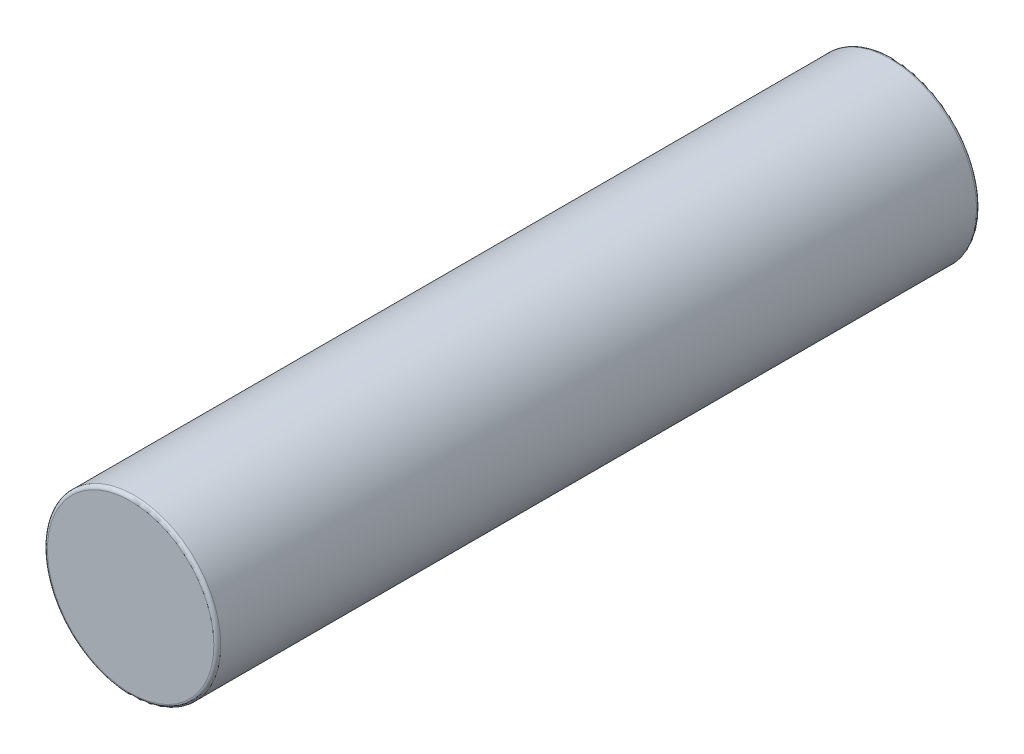
SolidWorks part; units mm, degrees
ref_plane "Front" through (0, 0, 0) normal (0, 0, 1) x (1, 0, 0)
ref_plane "Top" through (0, 0, 0) normal (0, 1, 0) x (1, 0, 0)
ref_plane "Right" through (0, 0, 0) normal (1, 0, 0) x (0, 0, -1)
sketch "Sketch1" plane through (0, 0, 0) normal (0, 0, 1) x (1, 0, 0)
  circle A0 centre (0, 0) radius 1.25
  dimension "D1" = 2.5
extrude "Boss-Extrude1" add sketch "Sketch1" along normal blind 11
fillet "Fillet1" radius 0.05 2 edges at (1.25, 0, 0) (1.25, 0, 11)
